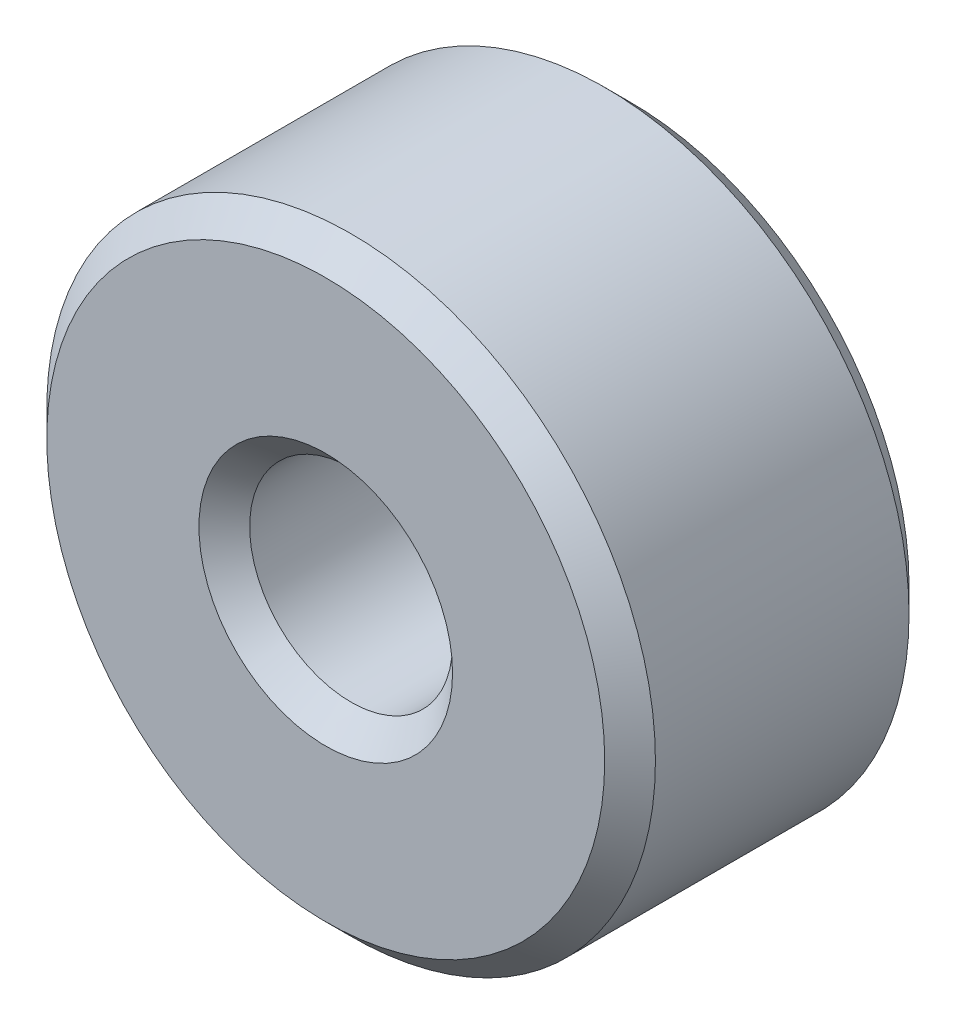
SolidWorks part; units mm, degrees
ref_plane "Front Plane" through (0, 0, 0) normal (0, 0, 1) x (1, 0, 0)
ref_plane "Top Plane" through (0, 0, 0) normal (0, 1, 0) x (1, 0, 0)
ref_plane "Right Plane" through (0, 0, 0) normal (1, 0, 0) x (0, 0, -1)
sketch "Sketch1" plane through (0, 0, 0) normal (0, 0, 1) x (1, 0, 0)
  circle A0 centre (0, 0) radius 1
  dimension "D1" = 2
extrude "Extrude-Thin1" add sketch "Sketch1" along normal blind 3 thin
chamfer "Chamfer1" distance 0.25 angle 45 4 edges at (1, 0, 0) (3, 0, 0) (1, 0, 3) (3, 0, 3)
